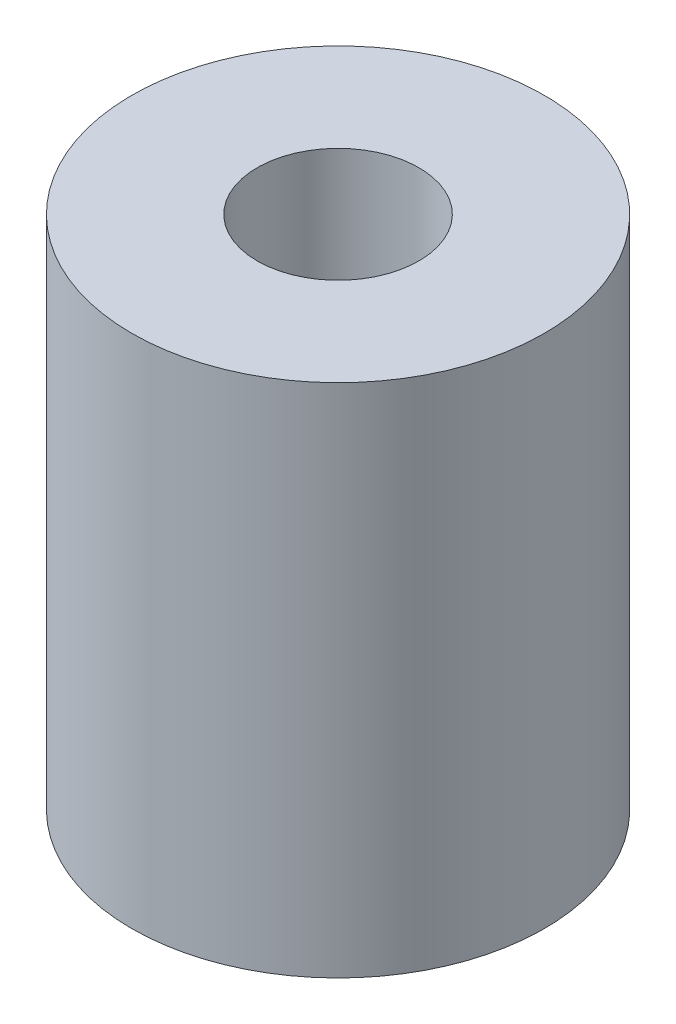
SolidWorks part; units mm, degrees
ref_plane "Front Plane" through (0, 0, 0) normal (0, 0, 1) x (1, 0, 0)
ref_plane "Top Plane" through (0, 0, 0) normal (0, 1, 0) x (1, 0, 0)
ref_plane "Right Plane" through (0, 0, 0) normal (1, 0, 0) x (0, 0, -1)
sketch "Sketch1" plane through (0, 0, 0) normal (0, 1, 0) x (1, 0, 0)
  circle A0 centre (0, 0) radius 6.35
  circle A1 centre (0, 0) radius 2.4892
  dimension "D1" = 12.7
  dimension "D2" = 4.9784
extrude "Boss-Extrude1" add sketch "Sketch1" along normal blind 15.875
